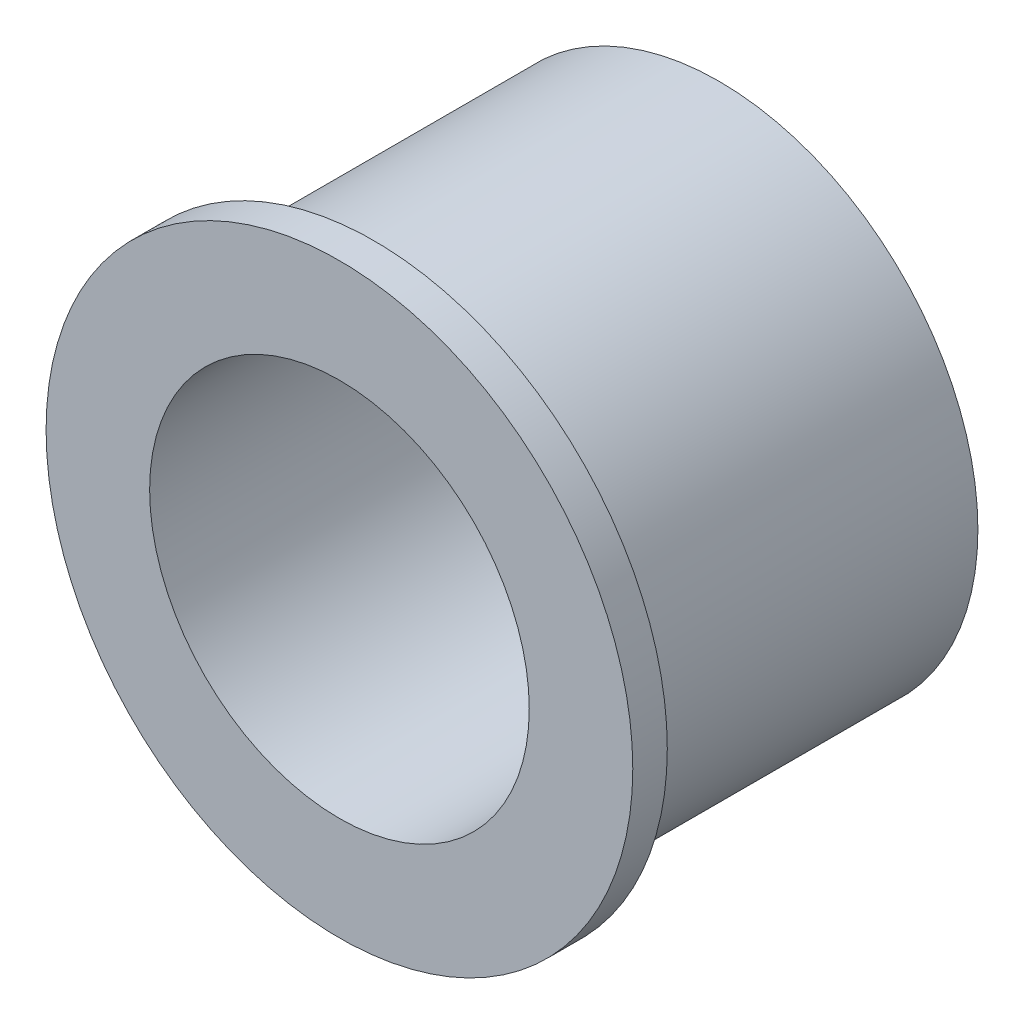
SolidWorks part; units mm, degrees
material "PET"
ref_plane "Front Plane" through (0, 0, 0) normal (0, 0, 1) x (1, 0, 0)
ref_plane "Top Plane" through (0, 0, 0) normal (0, 1, 0) x (1, 0, 0)
ref_plane "Right Plane" through (0, 0, 0) normal (1, 0, 0) x (0, 0, -1)
sketch "Sketch1" plane through (0, 0, 0) normal (0, 0, 1) x (1, 0, 0)
  circle A0 centre (0, 0) radius 27.5
  circle A1 centre (0, 0) radius 37.5
  dimension "D1" = 55
  dimension "D2" = 10
extrude "Boss-Extrude1" add sketch "Sketch1" along normal blind 50
sketch "Sketch2" plane through (0, 0, 50) normal (0, 0, 1) x (1, 0, 0)
  circle A0 centre (0, 0) radius 42.5
  circle A1 centre (0, 0) radius 27.5
  circle A2 centre (0, 0) radius 27.5 construction
  dimension "D1" = 85
extrude "Boss-Extrude2" add sketch "Sketch2" along normal blind 5
sketch "Sketch3" plane through (0, 0, 0) normal (0, 0, -1) x (-1, 0, 0)
  circle A0 centre (0, 0) radius 32.5 construction
  circle A1 centre (0, 0) radius 27.5 construction
  circle A2 centre (0, 32.5) radius 2
  circle A3 centre (22.981, 22.981) radius 2
  circle A4 centre (32.5, 0) radius 2
  circle A5 centre (22.981, -22.981) radius 2
  circle A6 centre (0, -32.5) radius 2
  circle A7 centre (-22.981, -22.981) radius 2
  circle A8 centre (-32.5, 0) radius 2
  circle A9 centre (-22.981, 22.981) radius 2
  point P23 (0, 0)
  dimension "D1" = 5
  dimension "D2" = 4
  dimension "D3" = 8
extrude "Cut-Extrude1" cut sketch "Sketch3" against normal blind 10
